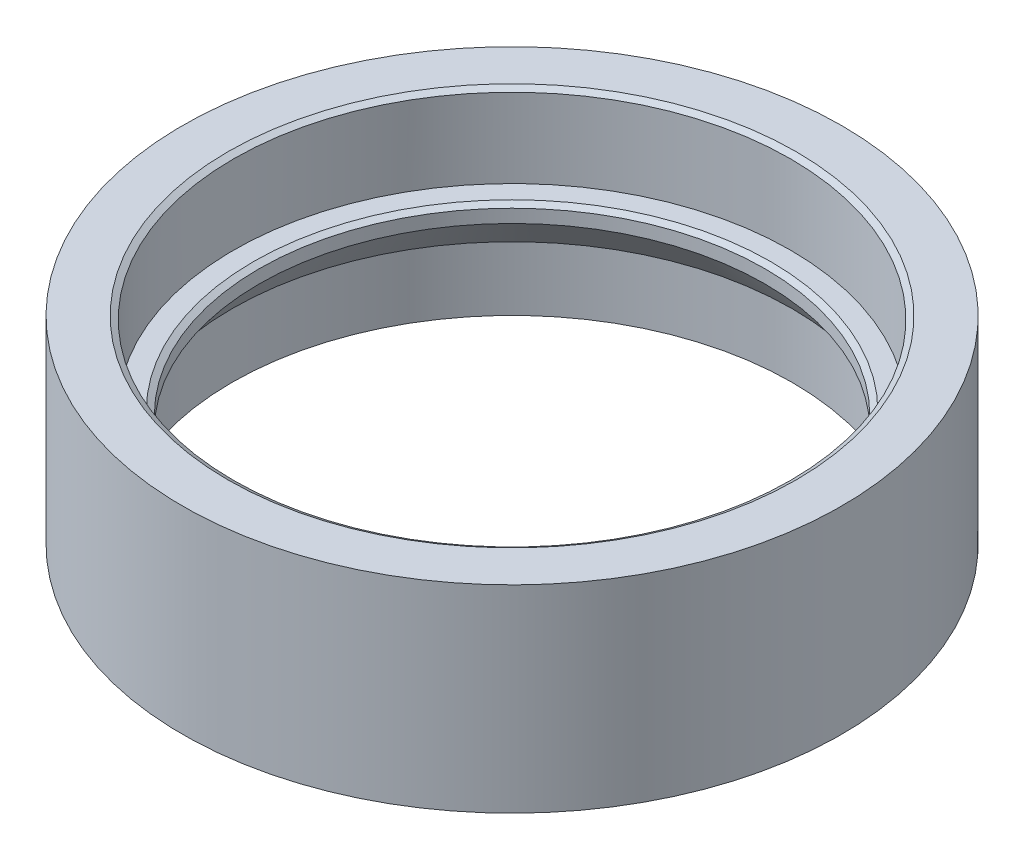
SolidWorks part; units mm, degrees
ref_plane "Front Plane" through (0, 0, 0) normal (0, 0, 1) x (1, 0, 0)
ref_plane "Top Plane" through (0, 0, 0) normal (0, 1, 0) x (1, 0, 0)
ref_plane "Right Plane" through (0, 0, 0) normal (1, 0, 0) x (0, 0, -1)
sketch "Sketch1" plane through (0, 0, 0) normal (0, 0, 1) x (1, 0, 0)
  line L1 (84.5, 60) -> (100, 60)
  line L2 (100, 60) -> (100, 0)
  line L3 (100, 0) -> (95, 0)
  line L4 (76.75, 35) -> (76.75, 30)
  line L5 (0, 0) -> (0, 60) construction
  line L6 (76.75, 35) -> (84.5, 35)
  line L7 (84.5, 35) -> (84.5, 60)
  line L10 (89.9, 0) -> (89.9, 5)
  line L11 (89.9, 5) -> (95, 5)
  line L12 (95, 0) -> (95, 5)
  line L13 (89.9, 0) -> (84.99, 0)
  line L14 (84.99, 19.3694) -> (76.75, 30)
  line L15 (0, 0) -> (30, 0) construction
  line L17 (84.99, 0) -> (84.99, 19.3694)
  point P2 (83.943, 20.7201)
  dimension "D1" = 76.75
  dimension "D2" = 100
  dimension "D3" = 60
  dimension "D4" = 84.99
  dimension "D5" = 84.5
  dimension "D7" = 5.1
  dimension "D8" = 5
  dimension "D9" = 5
  dimension "D11" = 142.22
  dimension "D12" = 5
  dimension "D13" = 35
  dimension "D14" = 30
revolve "Revolve1" add sketch "Sketch1" angle 360 about L5
chamfer "Chamfer2" distance 1 angle 60 2 edges at (0, 35, -76.75) (0, 60, -84.5)
fillet "Fillet1" radius 1 2 edges at (0, 0, -89.9) (0, 0, -95)
